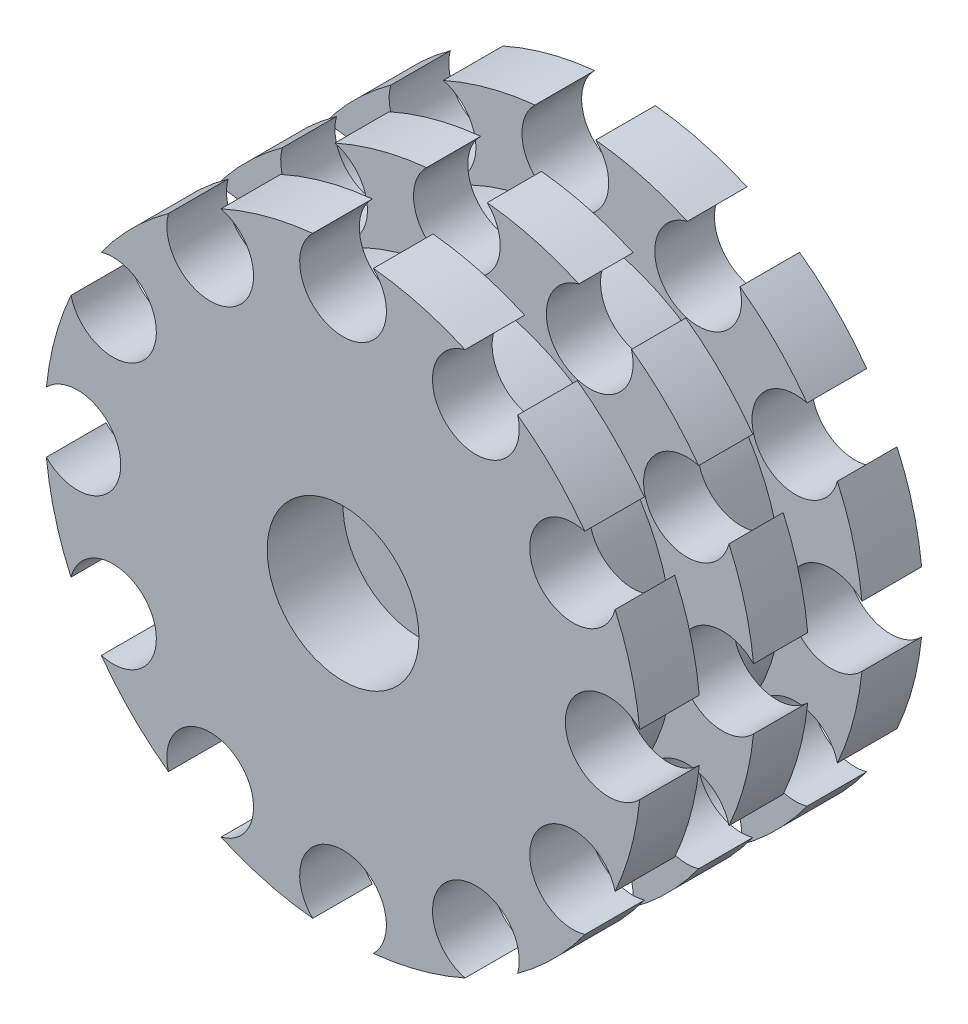
SolidWorks part; units mm, degrees
material "ABS"
ref_plane "Alzado" through (0, 0, 0) normal (0, 0, 1) x (1, 0, 0)
ref_plane "Planta" through (0, 0, 0) normal (0, 1, 0) x (1, 0, 0)
ref_plane "Vista lateral" through (0, 0, 0) normal (1, 0, 0) x (0, 0, -1)
sketch "Croquis1" plane through (0, 0, 0) normal (0, 1, 0) x (1, 0, 0)
  line L0 (0, 0) -> (0, 50000) construction
  line L1 (0, 1.5) -> (0, -9.5)
  line L3 (7, -9.5) -> (7, -13)
  line L4 (0, -9.5) -> (7, -9.5)
  line L5 (12.5, 13) -> (27.5, 13)
  line L6 (27.5, 13) -> (27.5, 7.5)
  line L7 (27.5, -2.5) -> (27.5, 2.5)
  line L8 (27.5, 2.5) -> (20, 2.5)
  line L9 (20, 2.5) -> (20, 7.5)
  line L10 (20, 7.5) -> (27.5, 7.5)
  line L12 (20, -7.5) -> (27.5, -7.5)
  line L13 (20, -2.5) -> (20, -7.5)
  line L14 (27.5, -2.5) -> (20, -2.5)
  line L15 (27.5, -13) -> (27.5, -7.5)
  line L16 (12.5, -13) -> (27.5, -13)
  line L27 (0, 1.5) -> (7.5, 1.5)
  line L28 (7.5, 1.5) -> (0, 1.5) construction
  line L29 (12.5, 6.5) -> (12.5, 13)
  line L32 (7, -13) -> (12.5, -13)
  line L37 (12.5, 6.5) -> (7.5, 1.5)
  line L38 (12.5, 6.5) -> (12.5, 13) construction
  point P22 (27.5, 0)
revolve "Revolución1" add sketch "Croquis1" angle 360 about L0
sketch "Croquis2" plane through (0, 0, -1.5) normal (0, 0, -1) x (-1, 0, 0)
  line L1 (7.5056, 0) -> (3.7528, 6.5)
  line L2 (3.7528, 6.5) -> (-3.7528, 6.5)
  line L3 (-3.7528, 6.5) -> (-7.5056, 0)
  line L4 (-7.5056, 0) -> (-3.7528, -6.5)
  line L5 (-3.7528, -6.5) -> (3.7528, -6.5)
  line L6 (3.7528, -6.5) -> (7.5056, 0)
  circle A0 centre (0, 0) radius 6.5 construction
extrude "Cortar-Extruir1" cut sketch "Croquis2" against normal blind 9
sketch "Croquis5" plane through (0, 0, 13) normal (0, 0, 1) x (1, 0, 0)
  line L0 (0, 0) -> (0, 27.5) construction
  line L1 (0, 27.5) -> (0, 24.5) construction
  circle A0 centre (0, 0) radius 27.5 construction
  circle A1 centre (0, 24.5) radius 4
  circle A2 centre (12.25, 21.2176) radius 4
  circle A3 centre (21.2176, 12.25) radius 4
  circle A4 centre (24.5, 0) radius 4
  circle A5 centre (21.2176, -12.25) radius 4
  circle A6 centre (12.25, -21.2176) radius 4
  circle A7 centre (0, -24.5) radius 4
  circle A8 centre (-12.25, -21.2176) radius 4
  circle A9 centre (-21.2176, -12.25) radius 4
  circle A10 centre (-24.5, 0) radius 4
  circle A11 centre (-21.2176, 12.25) radius 4
  circle A12 centre (-12.25, 21.2176) radius 4
  point P33 (0, 0)
  dimension "D1" = 12
extrude "Cortar-Extruir3" cut sketch "Croquis5" against normal through all
sketch "Croquis6" plane through (0, 0, 7.5) normal (0, 0, -1) x (-1, 0, 0)
  circle A0 centre (0, 0) radius 2
extrude "Cortar-Extruir4" cut sketch "Croquis6" against normal blind 10
sketch "Croquis7" plane through (0, 0, 7.5) normal (0, 0, -1) x (-1, 0, 0)
  line L6 (3.7528, -6.5) -> (7.5056, 0)
  line L7 (7.5056, 0) -> (3.7528, 6.5)
  line L8 (3.7528, 6.5) -> (-3.7528, 6.5)
  line L9 (-3.7528, 6.5) -> (-7.5056, 0)
  line L10 (-7.5056, 0) -> (-3.7528, -6.5)
  line L11 (-3.7528, -6.5) -> (3.7528, -6.5)
  line L12 (3.7528, -6.5) -> (7.5056, 0)
  line L13 (7.5056, 0) -> (3.7528, 6.5)
  line L14 (3.7528, 6.5) -> (-3.7528, 6.5)
  line L15 (-3.7528, 6.5) -> (-7.5056, 0)
  line L16 (-7.5056, 0) -> (-3.7528, -6.5)
  line L17 (-3.7528, -6.5) -> (3.7528, -6.5)
  circle A0 centre (0, 0) radius 2
  dimension "D1" = 0
extrude "Saliente-Extruir1" add sketch "Croquis7" along normal blind 3.5
sketch "Croquis8" plane through (0, 0, 9.5) normal (0, 0, 1) x (1, 0, 0)
  circle A0 centre (0, 0) radius 2
  circle A1 centre (0, 0) radius 7
extrude "Cortar-Extruir5" cut sketch "Croquis8" against normal blind 3.5
